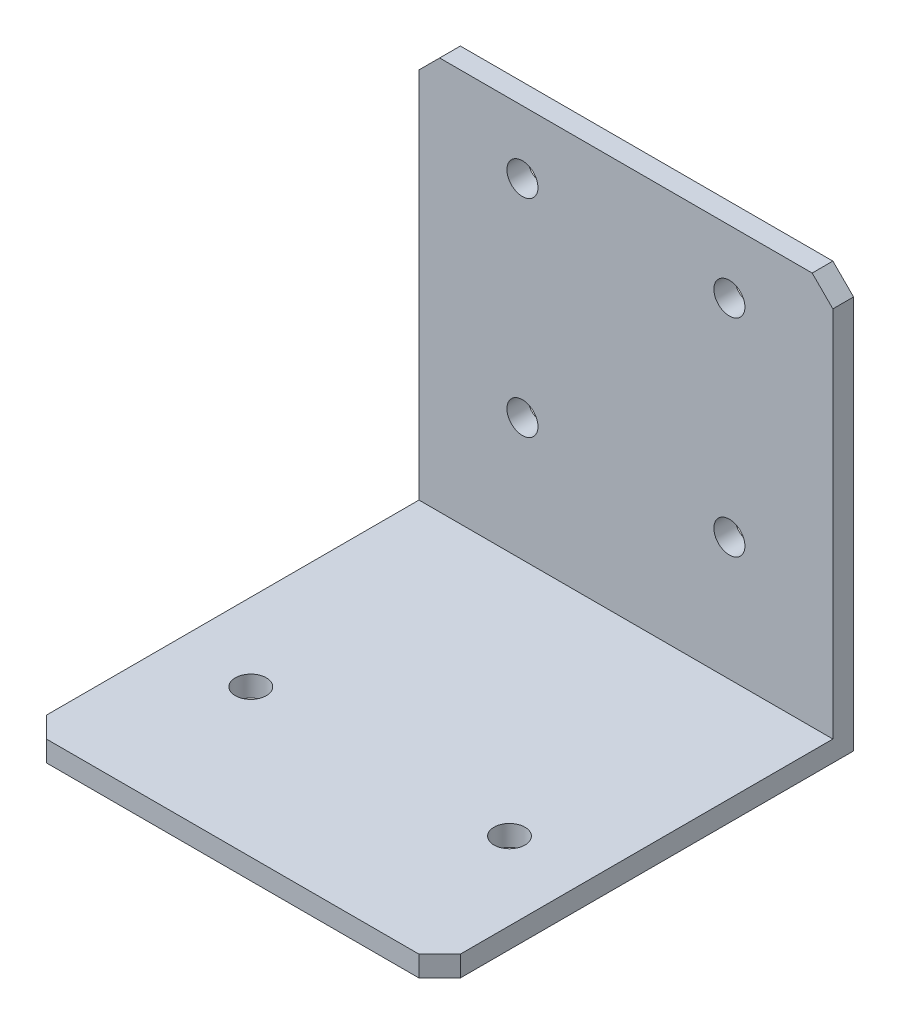
SolidWorks part; units mm, degrees
ref_plane "Спереди" through (0, 0, 0) normal (0, 0, 1) x (1, 0, 0)
ref_plane "Сверху" through (0, 0, 0) normal (0, 1, 0) x (1, 0, 0)
ref_plane "Справа" through (0, 0, 0) normal (1, 0, 0) x (0, 0, -1)
sketch "Sketch1" plane through (0, 0, 0) normal (1, 0, 0) x (0, 0, -1)
  line L0 (0, 0) -> (0, 38)
  line L1 (0, 38) -> (2, 38)
  line L2 (2, 38) -> (2, -2)
  line L3 (2, -2) -> (-38, -2)
  line L4 (-38, -2) -> (-38, 0)
  line L5 (-38, 0) -> (0, 0)
  dimension "D1" = 2
  dimension "D2" = 2
  dimension "D3" = 40
  dimension "D4" = 40
extrude "Extrude1" add sketch "Sketch1" along normal blind 40
sketch "Sketch2" plane through (0, -2, 0) normal (0, -1, 0) x (-1, 0, 0)
  line L0 (-40, 2) -> (0, 2) construction
  line L1 (-7.5, -23.75) -> (-32.5, -23.75) construction
  line L2 (-40, -38) -> (0, -38) construction
  circle A0 centre (-32.5, -23.75) radius 1.5
  circle A1 centre (-7.5, -23.75) radius 1.5
  point P5 (-20, -23.75)
  point P10 (-20, -38)
  dimension "D1" = 3
  dimension "D2" = 25
  dimension "D3" = 25.75
extrude "Extrude2" cut sketch "Sketch2" against normal up to next contours A0
sketch "Sketch3" plane through (0, 0, -2) normal (0, 0, -1) x (-1, 0, 0)
  line L1 (0, -2) -> (0, 38) construction
  line L2 (-40, 38) -> (0, 38) construction
  circle A0 centre (-10, 31.9) radius 1.5
  circle A1 centre (-30, 31.9) radius 1.5
  circle A2 centre (-30, 11.9) radius 1.5
  circle A3 centre (-10, 11.9) radius 1.5
  dimension "D1" = 10
  dimension "D2" = 6.1
  dimension "D3" = 2
  dimension "D4" = 2
extrude "Extrude3" cut sketch "Sketch3" against normal up to next
chamfer "Chamfer1" distance 2 angle 45 4 edges at (40, -1, 38) (0, -1, 38) (0, 38, -1) (40, 38, -1)
